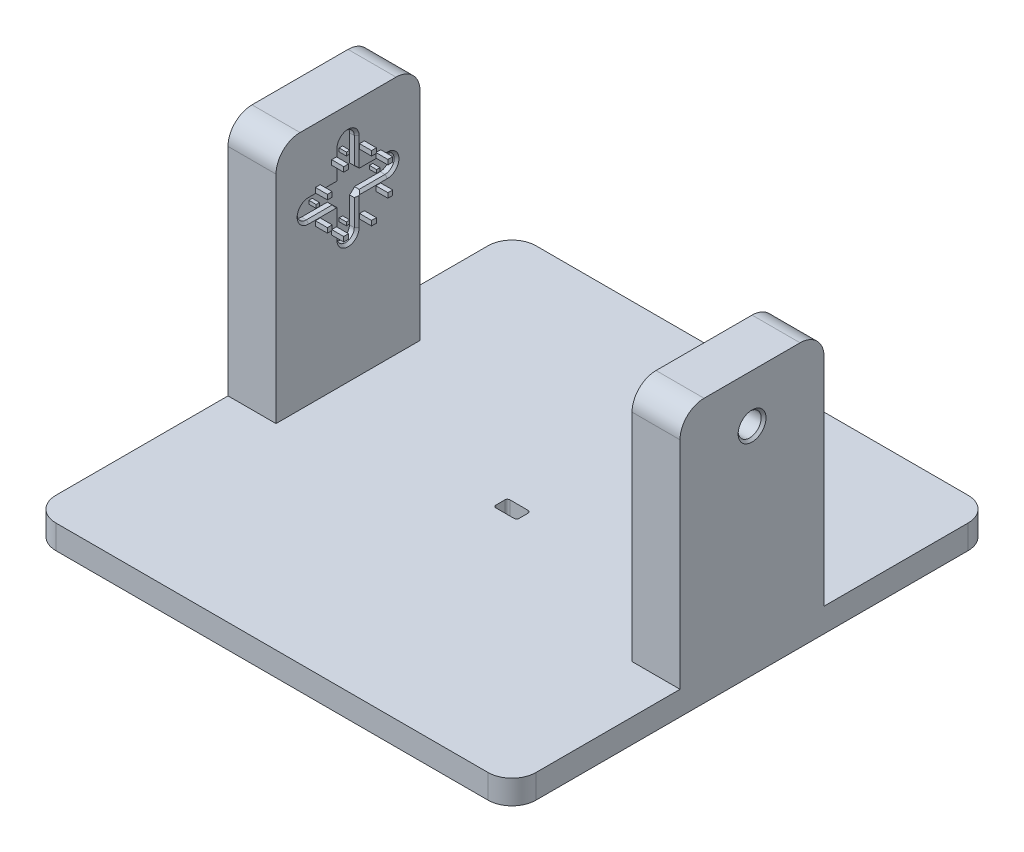
SolidWorks part; units mm, degrees
ref_plane "Front Plane" through (0, 0, 0) normal (0, 0, 1) x (1, 0, 0)
ref_plane "Top Plane" through (0, 0, 0) normal (0, 1, 0) x (1, 0, 0)
ref_plane "Right Plane" through (0, 0, 0) normal (1, 0, 0) x (0, 0, -1)
sketch "Sketch1" plane through (0, 0, 0) normal (0, 1, 0) x (1, 0, 0)
  line L1 (-50, -50) -> (50, -50)
  line L2 (-50, -50) -> (-50, 50)
  line L3 (-50, 50) -> (50, 50)
  line L4 (50, -50) -> (50, 50)
  line L5 (-50, -50) -> (50, 50) construction
  line L6 (-50, 50) -> (50, -50) construction
  point P0 (0, 0)
  dimension "D1" = 100
  dimension "D2" = 100
extrude "Boss-Extrude1" add sketch "Sketch1" along normal blind 5
sketch "Sketch2" plane through (0, 5, 0) normal (0, 1, 0) x (1, 0, 0)
  line L0 (-50, 50) -> (-50, -50) construction
  line L1 (-50, 20.85) -> (-40, 20.85)
  line L2 (-50, 20.85) -> (-50, -9.15)
  line L3 (-50, -9.15) -> (-40, -9.15)
  line L4 (-40, 20.85) -> (-40, -9.15)
  line L5 (0, 0) -> (0, 8.2707) construction
  line L6 (50, -15) -> (40, -15)
  line L7 (40, 15) -> (40, -15)
  line L8 (50, 15) -> (40, 15)
  line L9 (50, 15) -> (50, -15)
  line L10 (50, -50) -> (50, 50) construction
  point P13 (0, 0)
  point P16 (40, 0)
  dimension "D1" = 20.85
  dimension "D2" = 30
  dimension "D3" = 10
extrude "Boss-Extrude2" add sketch "Sketch2" along normal blind 50
sketch "Sketch4" plane through (0, 5, 0) normal (0, 1, 0) x (1, 0, 0)
  line L1 (-1.91, -1.46) -> (1.91, -1.46)
  line L2 (-2.41, -0.96) -> (-2.41, 0.96)
  line L3 (-1.91, 1.46) -> (1.91, 1.46)
  line L4 (2.41, -0.96) -> (2.41, 0.96)
  line L5 (-2.41, -1.46) -> (2.41, 1.46) construction
  line L6 (-2.41, 1.46) -> (2.41, -1.46) construction
  arc A0 (1.91, -1.46) -> (2.41, -0.96) centre (1.91, -0.96) ccw
  arc A1 (2.41, 0.96) -> (1.91, 1.46) centre (1.91, 0.96) ccw
  arc A2 (-2.41, -0.96) -> (-1.91, -1.46) centre (-1.91, -0.96) ccw
  arc A3 (-2.41, 0.96) -> (-1.91, 1.46) centre (-1.91, 0.96) cw
  point P0 (0, 0)
  dimension "D3" = 0.5
  dimension "D1" = 2.92
  dimension "D2" = 4.82
extrude "Cut-Extrude2" cut sketch "Sketch4" against normal through all
fillet "Fillet1" radius 5 4 edges at (50, 2.5, -50) (50, 2.5, 50) (-50, 2.5, 50) (-50, 2.5, -50)
fillet "Fillet2" radius 5 4 edges at (45, 55, 15) (45, 55, -15) (-45, 55, 9.15) (-45, 55, -20.85)
sketch "Sketch7" plane through (-40, 0, 0) normal (1, 0, 0) x (0, 0, -1)
  line L0 (-2.35, 40) -> (14.05, 40) construction
  line L1 (-2.35, 41.9) -> (14.05, 41.9)
  line L2 (-2.35, 38.1) -> (14.05, 38.1)
  line L3 (5.85, 31.7) -> (5.85, 48.3) construction
  line L4 (4.05, 31.7) -> (4.05, 48.3)
  line L5 (7.65, 31.7) -> (7.65, 48.3)
  line L6 (-9.15, 5) -> (20.85, 5) construction
  line L7 (5.85, 41.9) -> (5.85, 38.1)
  line L12 (-0.95, 37) -> (0.05, 37)
  line L13 (-0.95, 37) -> (-0.95, 38)
  line L18 (-0.95, 38) -> (0.05, 38)
  line L19 (0.05, 37) -> (0.05, 38)
  line L20 (-0.0964, 39.6464) -> (-0.8036, 39.6464)
  line L21 (-0.0964, 39.6464) -> (-0.0964, 40.3536)
  line L22 (-0.0964, 40.3536) -> (-0.8036, 40.3536)
  line L23 (-0.8036, 39.6464) -> (-0.8036, 40.3536)
  line L24 (-0.0964, 39.6464) -> (-0.8036, 40.3536) construction
  line L25 (-0.0964, 40.3536) -> (-0.8036, 39.6464) construction
  line L26 (5.4964, 45.9464) -> (6.2036, 45.9464)
  line L27 (5.4964, 45.9464) -> (5.4964, 46.6536)
  line L28 (5.4964, 46.6536) -> (6.2036, 46.6536)
  line L29 (6.2036, 45.9464) -> (6.2036, 46.6536)
  line L30 (5.4964, 45.9464) -> (6.2036, 46.6536) construction
  line L31 (5.4964, 46.6536) -> (6.2036, 45.9464) construction
  line L32 (9.7964, 39.6464) -> (10.5036, 39.6464)
  line L33 (9.7964, 39.6464) -> (9.7964, 40.3536)
  line L34 (9.7964, 40.3536) -> (10.5036, 40.3536)
  line L35 (10.5036, 39.6464) -> (10.5036, 40.3536)
  line L36 (9.7964, 39.6464) -> (10.5036, 40.3536) construction
  line L37 (9.7964, 40.3536) -> (10.5036, 39.6464) construction
  line L38 (5.4964, 35.3464) -> (6.2036, 35.3464)
  line L39 (5.4964, 35.3464) -> (5.4964, 36.0536)
  line L40 (5.4964, 36.0536) -> (6.2036, 36.0536)
  line L41 (6.2036, 35.3464) -> (6.2036, 36.0536)
  line L42 (5.4964, 35.3464) -> (6.2036, 36.0536) construction
  line L43 (5.4964, 36.0536) -> (6.2036, 35.3464) construction
  line L44 (-0.95, 37) -> (0.05, 38) construction
  line L45 (-0.95, 38) -> (0.05, 37) construction
  line L50 (4.05, 40) -> (7.65, 40)
  line L51 (11.65, 37) -> (11.65, 38)
  line L52 (2.95, 33.2) -> (3.95, 33.2)
  line L53 (2.95, 33.2) -> (2.95, 34.2)
  line L54 (2.95, 34.2) -> (3.95, 34.2)
  line L55 (3.95, 33.2) -> (3.95, 34.2)
  line L56 (2.95, 33.2) -> (3.95, 34.2) construction
  line L57 (2.95, 34.2) -> (3.95, 33.2) construction
  line L62 (8.75, 34.2) -> (7.75, 34.2)
  line L63 (7.75, 33.2) -> (7.75, 34.2)
  line L64 (12.65, 37) -> (11.65, 37)
  line L65 (12.65, 37) -> (12.65, 38)
  line L66 (12.65, 38) -> (11.65, 38)
  line L67 (12.65, 43) -> (11.65, 43)
  line L68 (12.65, 43) -> (12.65, 42)
  line L69 (12.65, 42) -> (11.65, 42)
  line L70 (11.65, 43) -> (11.65, 42)
  line L71 (-0.95, 43) -> (0.05, 43)
  line L72 (0.05, 43) -> (0.05, 42)
  line L73 (-0.95, 42) -> (0.05, 42)
  line L74 (-0.95, 43) -> (-0.95, 42)
  line L75 (8.75, 33.2) -> (7.75, 33.2)
  line L76 (5.4964, 33.3464) -> (6.2036, 33.3464)
  line L77 (5.4964, 33.3464) -> (5.4964, 34.0536)
  line L78 (5.4964, 34.0536) -> (6.2036, 34.0536)
  line L79 (6.2036, 33.3464) -> (6.2036, 34.0536)
  line L80 (5.4964, 33.3464) -> (6.2036, 34.0536) construction
  line L81 (5.4964, 34.0536) -> (6.2036, 33.3464) construction
  line L82 (11.7964, 39.6464) -> (12.5036, 39.6464)
  line L83 (11.7964, 39.6464) -> (11.7964, 40.3536)
  line L84 (11.7964, 40.3536) -> (12.5036, 40.3536)
  line L85 (12.5036, 39.6464) -> (12.5036, 40.3536)
  line L86 (11.7964, 39.6464) -> (12.5036, 40.3536) construction
  line L87 (11.7964, 40.3536) -> (12.5036, 39.6464) construction
  line L88 (8.75, 33.2) -> (8.75, 34.2)
  line L89 (8.75, 45.8) -> (7.75, 45.8)
  line L90 (8.75, 46.8) -> (8.75, 45.8)
  line L91 (7.75, 46.8) -> (7.75, 45.8)
  line L92 (8.75, 46.8) -> (7.75, 46.8)
  line L93 (2.95, 46.8) -> (3.95, 46.8)
  line L94 (3.95, 46.8) -> (3.95, 45.8)
  line L95 (2.95, 45.8) -> (3.95, 45.8)
  line L96 (2.95, 46.8) -> (2.95, 45.8)
  line L97 (-4.15, 55) -> (15.85, 55) construction
  line L98 (-4.15, 55) -> (15.85, 55)
  arc A0 (3.0304, 38.1) -> (4.05, 37.1156) centre (5.85, 40) ccw
  arc A1 (-2.35, 41.9) -> (-2.35, 38.1) centre (-2.35, 40) ccw
  arc A2 (14.05, 38.1) -> (14.05, 41.9) centre (14.05, 40) ccw
  arc A3 (4.05, 31.7) -> (7.65, 31.7) centre (5.85, 31.7) ccw
  arc A4 (7.65, 48.3) -> (4.05, 48.3) centre (5.85, 48.3) ccw
  arc A5 (4.05, 42.8844) -> (3.0304, 41.9) centre (5.85, 40) ccw
  arc A6 (8.6696, 41.9) -> (7.65, 42.8844) centre (5.85, 40) ccw
  arc A7 (7.65, 37.1156) -> (8.6696, 38.1) centre (5.85, 40) ccw
  circle A8 centre (5.85, 40) radius 4.3 construction
  circle A9 centre (5.85, 40) radius 6.3 construction
  circle A10 centre (5.85, 40) radius 8.3 construction
  circle A11 centre (1.55, 40) radius 0.5
  circle A12 centre (-0.45, 40) radius 0.5
  circle A13 centre (-2.45, 40) radius 0.5
  circle A14 centre (5.85, 44.3) radius 0.5
  circle A15 centre (5.85, 46.3) radius 0.5
  circle A16 centre (5.85, 48.3) radius 0.5
  circle A17 centre (10.15, 40) radius 0.5
  circle A18 centre (12.15, 40) radius 0.5
  circle A19 centre (14.15, 40) radius 0.5
  circle A20 centre (5.85, 35.7) radius 0.5
  circle A21 centre (5.85, 33.7) radius 0.5
  circle A22 centre (5.85, 31.7) radius 0.5
  point P0 (5.85, 40)
  point P32 (-0.45, 37.5)
  point P43 (5.85, 40)
  point P65 (3.45, 33.7)
  point P83 (5.85, 40)
  point P89 (15.95, 40)
  point P90 (-4.25, 40)
  point P91 (5.85, 50.1)
  point P92 (5.85, 29.9)
  point P120 (0, 40)
  point P121 (0, 40)
  point P122 (0, 40)
  point P123 (2.2181, 40)
  point P124 (6.0688, 40)
  point P127 (5.85, 55)
  line M1 (15.85, 55) -> (-4.15, 55)
  line M3 (-9.15, 50) -> (-9.15, 5)
  line M5 (20.85, 5) -> (20.85, 50)
  dimension "D1" = 6.8
  dimension "D2" = 20.2
  dimension "D3" = 20.2
  dimension "D4" = 1
  dimension "D5" = 1.9
  dimension "D7" = 8.6
  dimension "D8" = 12.6
  dimension "D9" = 16.6
  dimension "D10" = 1
  dimension "D11" = 1
  dimension "D12" = 1
  dimension "D6" = 35
  dimension "D13" = 1
  dimension "D14" = 0.1
  dimension "D15" = 0.1
extrude "Cut-Extrude3" cut sketch "Sketch7" against normal blind 1.5 contours L1 A1 L2 L4 M3 | L2 L5 L1 L4 | L4 A5 L1 | L5 A4 L4 L1 M1 | A2 L1 L5 L2 M5 | L5 A7 L2 | L2 A0 L4 | L4 A3 L5 L2 | L1 A6 L5 | L7 L50 L5 L1 | L50 L4 L2 L7 | L50 L7 L2 L5 | A13 | A11 | L21 A12 | L22 A12 | L23 A12 | L20 A12 | A19 | L32 L35 L34 L33 | L35 A17 | L34 A17 | L33 A17 | L32 A17 | L82 A18 | L83 A18 | L84 A18 | L85 A18 | A22 | L41 A20 | L38 L41 L40 L39 | L40 A20 | L39 A20 | L38 A20 | L78 A21 | L77 A21 | L76 A21 | L79 A21 | A14 | A16 | L29 A15 | L26 A15 | L27 A15 | L28 A15
sketch "Sketch10" plane through (40, 0, 0) normal (-1, 0, 0) x (0, 0, 1)
  line L0 (-10, 55) -> (10, 55) construction
  line L1 (-15, 50) -> (-15, 5) construction
  circle A1 centre (0, 45) radius 2.4
  point P0 (0, 0)
  point P3 (-5, 45)
  dimension "D3" = 4.8
  dimension "D1" = 10
  dimension "D2" = 15
extrude "Cut-Extrude4" cut sketch "Sketch10" against normal through all
chamfer "Chamfer1" distance 0.5 angle 45 8 edges at (0, 0, 1.46) (0, 0, -1.46) (2.2636, 0, 1.3136) (-2.2636, 0, 1.3136) (2.41, 0, 0) (-2.41, 0, 0) (2.2636, 0, -1.3136) (-2.2636, 0, -1.3136)
chamfer "Chamfer2" distance 0.5 angle 45 12 edges at (-40, 40, -15.95) (-40, 41.9, -11.3598) (-40, 34.4078, -4.05) (-40, 29.9, -5.85) (-40, 34.4078, -7.65) (-40, 40, 4.25) (-40, 38.1, -0.3402) (-40, 50.1, -5.85) (-40, 45.5922, -4.05) (-40, 38.1, -11.3598) (-40, 41.9, -0.3402) (-40, 45.5922, -7.65)
chamfer "Chamfer3" distance 0.5 angle 45 1 edges at (50, 45, 2.4)
sketch "Sketch11" plane through (-40, 0, 0) normal (1, 0, 0) x (0, 0, -1)
  line L0 (6.2036, 34.0536) -> (5.4964, 34.0536) construction
  line L1 (-0.95, 36.5) -> (0.05, 36.5)
  line L2 (-0.95, 36.5) -> (-0.95, 37.5)
  line L3 (-0.95, 37.5) -> (0.05, 37.5)
  line L4 (0.05, 36.5) -> (0.05, 37.5)
  line L5 (-0.95, 36.5) -> (0.05, 37.5) construction
  line L6 (-0.95, 37.5) -> (0.05, 36.5) construction
  line L7 (2.45, 33.2) -> (3.45, 33.2)
  line L8 (2.45, 33.2) -> (2.45, 34.2)
  line L9 (2.45, 34.2) -> (3.45, 34.2)
  line L10 (3.45, 33.2) -> (3.45, 34.2)
  line L11 (2.45, 33.2) -> (3.45, 34.2) construction
  line L12 (2.45, 34.2) -> (3.45, 33.2) construction
  line L13 (5.4964, 34.0536) -> (5.4964, 33.3464) construction
  line L14 (5.4964, 33.3464) -> (6.2036, 33.3464) construction
  line L15 (6.2036, 33.3464) -> (6.2036, 34.0536) construction
  line L16 (-0.0964, 40.3536) -> (-0.8036, 40.3536) construction
  line L17 (-0.8036, 40.3536) -> (-0.8036, 39.6464) construction
  line L18 (-0.8036, 39.6464) -> (-0.0964, 39.6464) construction
  line L19 (-0.0964, 39.6464) -> (-0.0964, 40.3536) construction
  line L20 (6.2036, 34.0536) -> (5.4964, 34.0536)
  line L21 (5.4964, 34.0536) -> (5.4964, 33.3464)
  line L22 (5.4964, 33.3464) -> (6.2036, 33.3464)
  line L23 (6.2036, 33.3464) -> (6.2036, 34.0536)
  line L24 (-0.0964, 40.3536) -> (-0.8036, 40.3536)
  line L25 (-0.8036, 40.3536) -> (-0.8036, 39.6464)
  line L26 (-0.8036, 39.6464) -> (-0.0964, 39.6464)
  line L27 (-0.0964, 39.6464) -> (-0.0964, 40.3536)
  line L28 (3.4417, 37.6) -> (-2.35, 37.6) construction
  line L29 (3.55, 31.7) -> (3.55, 37.496) construction
  line L30 (-0.8036, 40.3536) -> (-0.0964, 39.6464)
  line L31 (-0.0964, 40.3536) -> (-0.8036, 39.6464)
  line L32 (5.4964, 34.0536) -> (6.2036, 33.3464)
  line L33 (5.4964, 33.3464) -> (6.2036, 34.0536)
  line L34 (5.85, 33.3464) -> (5.85, 34.0536)
  line L35 (-0.8036, 40) -> (-0.0964, 40)
  line L36 (-0.95, 43.5) -> (0.05, 43.5)
  line L37 (-0.95, 43.5) -> (-0.95, 42.5)
  line L38 (-0.95, 42.5) -> (0.05, 42.5)
  line L39 (0.05, 43.5) -> (0.05, 42.5)
  line L40 (11.65, 36.5) -> (11.65, 37.5)
  line L41 (12.65, 36.5) -> (11.65, 36.5)
  line L42 (12.65, 36.5) -> (12.65, 37.5)
  line L43 (12.65, 37.5) -> (11.65, 37.5)
  line L44 (12.65, 42.5) -> (11.65, 42.5)
  line L45 (11.65, 43.5) -> (11.65, 42.5)
  line L46 (12.65, 43.5) -> (11.65, 43.5)
  line L47 (12.65, 43.5) -> (12.65, 42.5)
  line L48 (8.25, 33.2) -> (8.25, 34.2)
  line L49 (9.25, 34.2) -> (8.25, 34.2)
  line L50 (9.25, 33.2) -> (9.25, 34.2)
  line L51 (9.25, 33.2) -> (8.25, 33.2)
  line L52 (9.25, 46.8) -> (8.25, 46.8)
  line L53 (9.25, 46.8) -> (9.25, 45.8)
  line L54 (9.25, 45.8) -> (8.25, 45.8)
  line L55 (8.25, 46.8) -> (8.25, 45.8)
  line L56 (2.45, 45.8) -> (3.45, 45.8)
  line L57 (3.45, 46.8) -> (3.45, 45.8)
  line L58 (2.45, 46.8) -> (3.45, 46.8)
  line L59 (2.45, 46.8) -> (2.45, 45.8)
  point P0 (-0.45, 37)
  point P5 (2.95, 33.7)
  point P22 (-0.45, 40)
  point P23 (5.85, 33.7)
  dimension "D1" = 1
  dimension "D2" = 1
  dimension "D3" = 1
  dimension "D4" = 0.1
  dimension "D5" = 0.1
extrude "Boss-Extrude3" add sketch "Sketch11" along normal blind 2.5 contours L58 L59 L56 L57 | L52 L55 L54 L53 | L47 L46 L45 L44 | L42 L43 L40 L41 | L51 L50 L49 L48 | L7 L10 L9 L8 | L1 L4 L3 L2 | L39 L36 L37 L38
